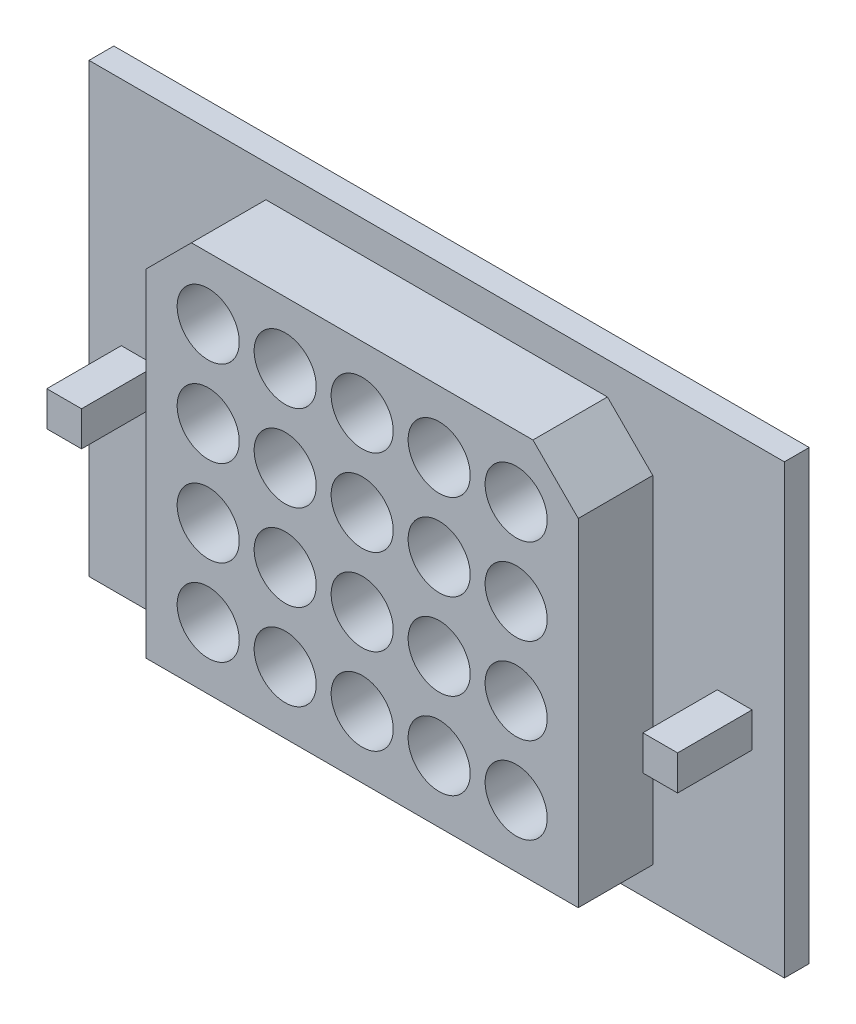
SolidWorks part; units mm, degrees
ref_plane "Front Plane" through (0, 0, 0) normal (0, 0, 1) x (1, 0, 0)
ref_plane "Top Plane" through (0, 0, 0) normal (0, 1, 0) x (1, 0, 0)
ref_plane "Right Plane" through (0, 0, 0) normal (1, 0, 0) x (0, 0, -1)
sketch "Sketch1" plane through (0, 0, 0) normal (0, 0, 1) x (1, 0, 0)
  line L1 (-15.2366, 7.7588) -> (12.7634, 7.7588)
  line L2 (-15.2366, 7.7588) -> (-15.2366, -10.2412)
  line L3 (-15.2366, -10.2412) -> (12.7634, -10.2412)
  line L4 (12.7634, 7.7588) -> (12.7634, -10.2412)
  dimension "D1" = 28
  dimension "D2" = 18
extrude "Boss-Extrude1" add sketch "Sketch1" along normal blind 1
sketch "Sketch2" plane through (0, 0, 1) normal (0, 0, 1) x (1, 0, 0)
  line L0 (-1.2366, 7.7588) -> (-1.2366, -10.2412) construction
  line L1 (12.7634, 7.7588) -> (-15.2366, 7.7588) construction
  line L2 (-15.2366, -10.2412) -> (12.7634, -10.2412) construction
  line L3 (-15.2366, -1.2412) -> (12.7634, -1.2412) construction
  line L4 (-15.2366, 7.7588) -> (-15.2366, -10.2412) construction
  line L5 (12.7634, -10.2412) -> (12.7634, 7.7588) construction
  line L7 (-14.2366, -1.2412) -> (-12.2366, -1.2412) construction
  line L8 (-14.2366, -1.2412) -> (-14.2366, -3.2412) construction
  line L9 (-14.2366, -3.2412) -> (-12.2366, -3.2412) construction
  line L10 (-12.2366, -1.2412) -> (-12.2366, -3.2412) construction
  line L11 (11.7634, -1.2412) -> (9.7634, -1.2412) construction
  line L12 (11.7634, -1.2412) -> (11.7634, -3.2412) construction
  line L13 (11.7634, -3.2412) -> (9.7634, -3.2412) construction
  line L14 (9.7634, -1.2412) -> (9.7634, -3.2412) construction
  line L15 (-10.2366, 6.7588) -> (7.7634, 6.7588) construction
  line L16 (-10.2366, 6.7588) -> (-10.2366, -9.2412) construction
  line L17 (-10.2366, -9.2412) -> (7.7634, -9.2412) construction
  line L18 (7.7634, 6.7588) -> (7.7634, -9.2412) construction
  line L22 (11.4634, -1.5412) -> (10.0634, -1.5412)
  line L23 (10.0634, -1.5412) -> (10.0634, -2.9412)
  line L24 (11.4634, -2.9412) -> (10.0634, -2.9412)
  line L25 (11.4634, -1.5412) -> (11.4634, -2.9412)
  line L30 (-13.9366, -1.5412) -> (-12.5366, -1.5412)
  line L31 (-12.5366, -1.5412) -> (-12.5366, -2.9412)
  line L32 (-13.9366, -2.9412) -> (-12.5366, -2.9412)
  line L33 (-13.9366, -1.5412) -> (-13.9366, -2.9412)
  line L34 (5.7634, 6.7588) -> (7.7634, 4.7588) construction
  line L35 (-10.2366, 4.7588) -> (-8.2366, 6.7588) construction
  line L36 (-8.1124, 6.4588) -> (5.6391, 6.4588)
  line L37 (7.4634, 4.6345) -> (7.4634, -8.9412)
  line L38 (-9.9366, -8.9412) -> (7.4634, -8.9412)
  line L39 (-9.9366, 4.6345) -> (-9.9366, -8.9412)
  line L40 (-9.9366, 4.6345) -> (-8.1124, 6.4588)
  line L41 (5.6391, 6.4588) -> (7.4634, 4.6345)
  line L42 (7.4634, 6.4588) -> (7.4634, -8.9412) construction
  line L43 (-9.9366, 6.4588) -> (7.4634, 6.4588) construction
  line L44 (-9.9366, 6.4588) -> (-9.9366, -8.9412) construction
  line L45 (-10.0245, 4.5466) -> (-8.0245, 6.5466) construction
  line L46 (5.5512, 6.5466) -> (7.5512, 4.5466) construction
  point P26 (-1.2366, 6.7588)
  point P27 (-10.2366, -1.2412)
  dimension "D1" = 2
  dimension "D2" = 2
  dimension "D3" = 6
  dimension "D4" = 2
  dimension "D5" = 2
  dimension "D6" = 6
  dimension "D7" = 18
  dimension "D8" = 16
  dimension "D9" = 0
  dimension "D10" = 0
  dimension "D12" = 2
  dimension "D13" = 2
  dimension "D11" = 135
  dimension "D16" = 135
  dimension "D17" = 2
  dimension "D18" = 2
  dimension "D14" = 0.3
  dimension "D15" = 0.3
  dimension "D19" = 0.3
  dimension "D20" = 0.3
extrude "Boss-Extrude3" add sketch "Sketch2" along normal blind 3
sketch "Sketch3" plane through (0, 0, 4) normal (0, 0, 1) x (1, 0, 0)
  line L5 (5.6391, 6.4588) -> (-8.1124, 6.4588) construction
  line L6 (-9.9366, 4.6345) -> (-9.9366, -8.9412) construction
  line L7 (7.4634, -8.9412) -> (7.4634, 4.6345) construction
  line L8 (-9.9366, -8.9412) -> (7.4634, -8.9412) construction
  line L9 (7.4634, -8.9412) -> (7.4634, 4.6345) construction
  circle A29 centre (-7.4366, 3.9588) radius 1.25
  circle A30 centre (-4.3366, 3.9588) radius 1.25
  circle A31 centre (-1.2366, 3.9588) radius 1.25
  circle A32 centre (1.8634, 3.9588) radius 1.25
  circle A33 centre (4.9634, 3.9588) radius 1.25
  circle A34 centre (-4.3366, 0.4921) radius 1.25
  circle A35 centre (-1.2366, 0.4921) radius 1.25
  circle A36 centre (1.8634, 0.4921) radius 1.25
  circle A37 centre (4.9634, 0.4921) radius 1.25
  circle A38 centre (-4.3366, -2.9746) radius 1.25
  circle A39 centre (-1.2366, -2.9746) radius 1.25
  circle A40 centre (1.8634, -2.9746) radius 1.25
  circle A41 centre (4.9634, -2.9746) radius 1.25
  circle A42 centre (-4.3366, -6.4412) radius 1.25
  circle A43 centre (-1.2366, -6.4412) radius 1.25
  circle A44 centre (1.8634, -6.4412) radius 1.25
  circle A45 centre (4.9634, -6.4412) radius 1.25
  circle A46 centre (-7.4366, 0.4921) radius 1.25
  circle A47 centre (-7.4366, -2.9746) radius 1.25
  circle A48 centre (-7.4366, -6.4412) radius 1.25
  dimension "D2" = 2.5
  dimension "D1" = 2.5
  dimension "D3" = 2.5
  dimension "D4" = 2.5
  dimension "D5" = 2.5
  dimension "D6" = 2.5
extrude "Cut-Extrude1" cut sketch "Sketch3" against normal blind 10
